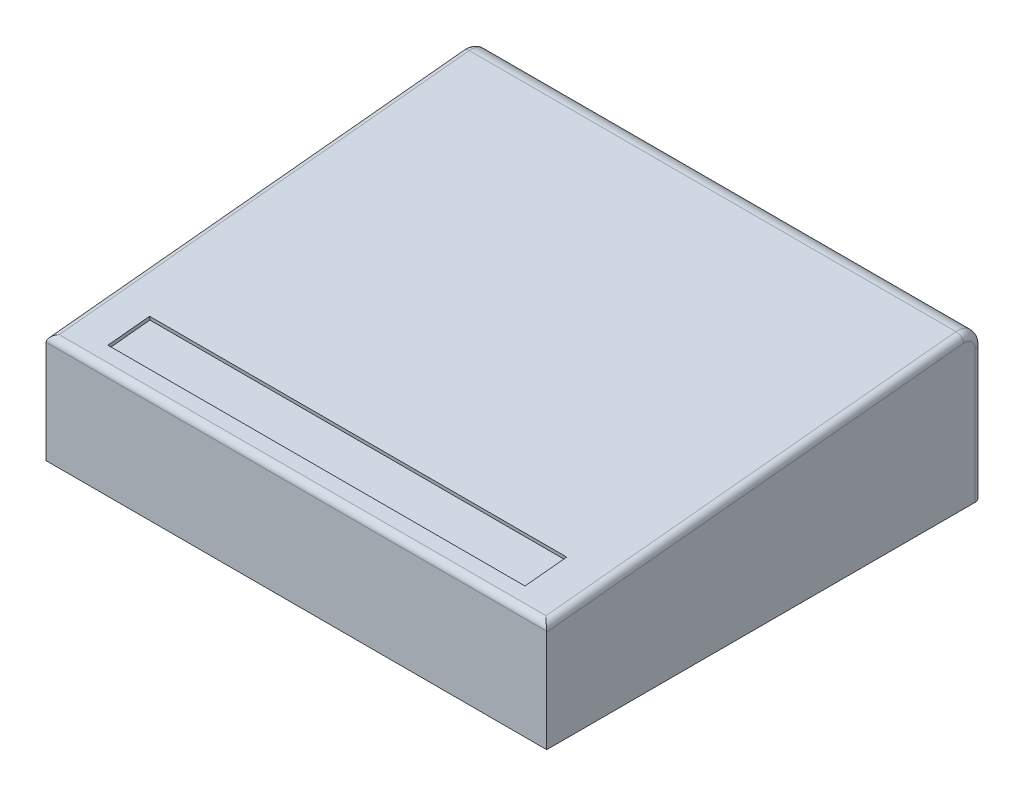
SolidWorks part; units mm, degrees
material "PE High Density"
ref_plane "Front Plane" through (0, 0, 0) normal (0, 0, 1) x (1, 0, 0)
ref_plane "Top Plane" through (0, 0, 0) normal (0, 1, 0) x (1, 0, 0)
ref_plane "Right Plane" through (0, 0, 0) normal (1, 0, 0) x (0, 0, -1)
sketch "Sketch1" plane through (0, 0, 0) normal (1, 0, 0) x (0, 0, -1)
  line L0 (0, 0) -> (15.875, 0)
  line L1 (15.875, 0) -> (15.875, 5.5562)
  line L2 (0, 0) -> (0, 3.9688)
  line L3 (0, 3.9688) -> (15.875, 5.5562)
  dimension "D1" = 3.9688
  dimension "D2" = 5.5562
  dimension "D3" = 15.875
extrude "Boss-Extrude1" add sketch "Sketch1" along normal blind 18.2562
fillet "Fillet1" radius 0.635 1 edges at (9.1281, 5.5562, -15.875)
fillet "Fillet2" radius 0.254 7 edges at (18.2562, 5.3254, -15.6661) (0, 5.3254, -15.6661) (9.1281, 3.9688, 0) (18.2562, 4.7276, -7.5884) (0, 4.7276, -7.5884) (18.2562, 2.4273, -15.875) (0, 2.4273, -15.875)
sketch "Sketch2" plane through (0, 3.9295, 0.3929) normal (0, 0.995, 0.0995) x (1, 0, 0)
  line L0 (0.254, 0.6248) -> (18.0022, 0.6248) construction
  line L1 (16.7322, 2.659) -> (1.524, 2.659)
  line L2 (16.7322, 2.659) -> (16.7322, 1.1305)
  line L3 (16.7322, 1.1305) -> (1.524, 1.1305)
  line L4 (1.524, 2.659) -> (1.524, 1.1305)
  line L5 (16.7322, 2.659) -> (1.524, 1.1305) construction
  line L6 (16.7322, 1.1305) -> (1.524, 2.659) construction
  line L7 (18.0022, 0.6248) -> (18.0022, 15.6474) construction
  point P0 (9.1281, 1.8948)
  point P5 (0, 0)
  point P8 (9.1281, 0.6248)
  dimension "D1" = 1.27
  dimension "D2" = 1.27
  dimension "D3" = 15.2082
extrude "Cut-Extrude1" cut sketch "Sketch2" against normal blind 0.127
